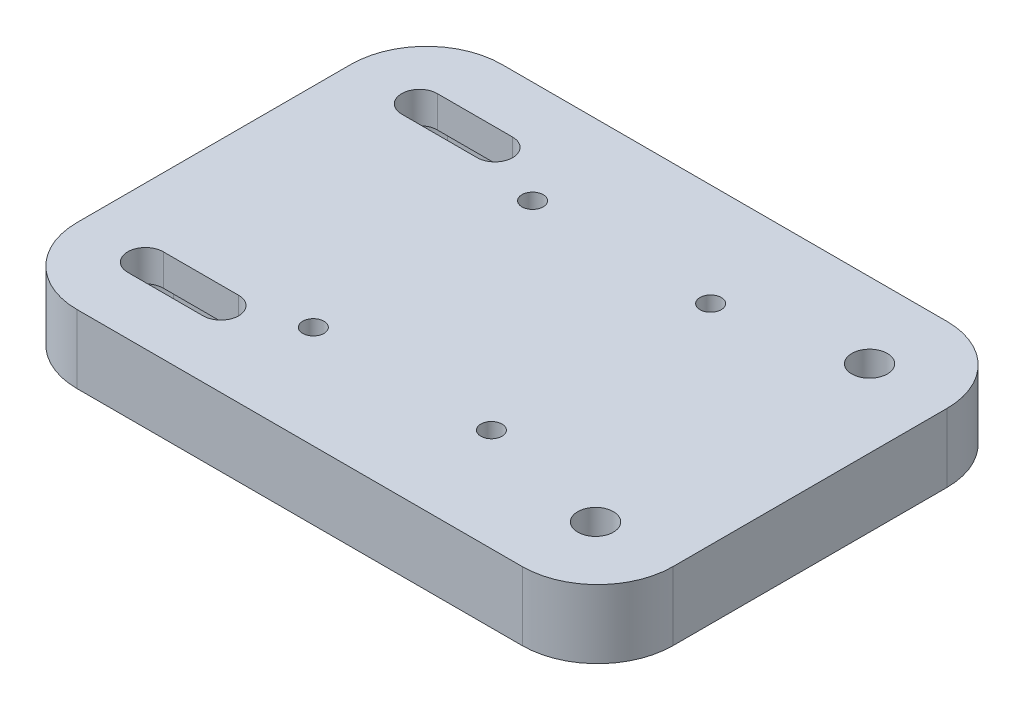
SolidWorks part; units mm, degrees
material "ABS"
ref_plane "Front Plane" through (0, 0, 0) normal (0, 0, 1) x (1, 0, 0)
ref_plane "Top Plane" through (0, 0, 0) normal (0, 1, 0) x (1, 0, 0)
ref_plane "Right Plane" through (0, 0, 0) normal (1, 0, 0) x (0, 0, -1)
sketch "Sketch1" plane through (0, 0, 0) normal (0, 1, 0) x (1, 0, 0)
  line L0 (0, 11) -> (0, 51)
  line L1 (11, 62) -> (76, 62)
  line L2 (87, 51) -> (87, 11)
  line L3 (76, 0) -> (11, 0)
  line L4 (0, 11) -> (0, 0) construction
  line L5 (0, 0) -> (11, 0) construction
  arc A0 (11, 62) -> (0, 51) centre (11, 51) ccw
  arc A1 (0, 11) -> (11, 0) centre (11, 11) ccw
  arc A2 (76, 0) -> (87, 11) centre (76, 11) ccw
  arc A3 (87, 51) -> (76, 62) centre (76, 51) ccw
  dimension "D3" = 22
  dimension "D1" = 87
  dimension "D2" = 62
extrude "Boss-Extrude1" add sketch "Sketch1" along normal blind 10
sketch "Sketch8" plane through (0, 10, 0) normal (0, 1, 0) x (1, 0, 0)
  line L0 (76, 62) -> (11, 62) construction
  line L1 (0, 51) -> (0, 11) construction
  line L2 (11, 0) -> (76, 0) construction
  line L3 (10, 53.6) -> (21, 53.6)
  line L4 (10, 48.4) -> (21, 48.4)
  line L5 (10, 13.6) -> (21, 13.6)
  line L6 (21, 8.4) -> (10, 8.4)
  circle A0 centre (75.7, 51) radius 2.6
  circle A1 centre (75.7, 11) radius 2.6
  arc A2 (21, 48.4) -> (21, 53.6) centre (21, 51) ccw
  arc A3 (10, 53.6) -> (10, 48.4) centre (10, 51) ccw
  arc A4 (21, 8.4) -> (21, 13.6) centre (21, 11) ccw
  arc A5 (10, 13.6) -> (10, 8.4) centre (10, 11) ccw
  point P11 (43.5, 62)
  dimension "D1" = 5.2
  dimension "D2" = 11
  dimension "D3" = 10
  dimension "D4" = 32.2
  dimension "D5" = 11
  dimension "D6" = 11
extrude "Cut-Extrude5" cut sketch "Sketch8" against normal up to next
sketch "Sketch9" plane through (0, 0, 0) normal (0, -1, 0) x (1, 0, 0)
  line L0 (10, -6.9) -> (21, -6.9)
  line L1 (21, -15.1) -> (10, -15.1)
  line L2 (10, -46.9) -> (21, -46.9)
  line L3 (21, -55.1) -> (10, -55.1)
  line L4 (6.959, -13.75) -> (3, -13.75)
  line L5 (3, -13.75) -> (3, -8.25)
  line L6 (3, -8.25) -> (6.959, -8.25)
  line L7 (6.959, -53.75) -> (3, -53.75)
  line L8 (3, -53.75) -> (3, -48.25)
  line L9 (0, -51) -> (0, -11) construction
  line L10 (3, -48.25) -> (6.959, -48.25)
  circle A0 centre (75.7, -11) radius 4.1
  circle A1 centre (75.7, -51) radius 4.1
  arc A2 (21, -55.1) -> (21, -46.9) centre (21, -51) ccw
  arc A3 (10, -46.9) -> (6.959, -48.25) centre (10, -51) ccw
  arc A4 (21, -15.1) -> (21, -6.9) centre (21, -11) ccw
  arc A5 (10, -6.9) -> (6.959, -8.25) centre (10, -11) ccw
  arc A6 (6.959, -53.75) -> (10, -55.1) centre (10, -51) ccw
  arc A7 (6.959, -13.75) -> (10, -15.1) centre (10, -11) ccw
  dimension "D1" = 8.2
  dimension "D2" = 5.5
  dimension "D3" = 3
  dimension "D4" = 3
extrude "Cut-Extrude6" cut sketch "Sketch9" against normal blind 5.4
sketch "Sketch11" plane through (0, 0, 0) normal (-1, 0, 0) x (0, 0, 1)
  line L0 (-11, 10) -> (-11, 0) construction
  line L1 (-51, 10) -> (-51, 0) construction
  circle A0 centre (-11, 5) radius 1.6
  circle A1 centre (-51, 5) radius 1.6
  dimension "D1" = 3.2
extrude "Cut-Extrude7" cut sketch "Sketch11" against normal up to next
sketch "Sketch12" plane through (3, 0, 0) normal (1, 0, 0) x (0, 0, -1)
  line L1 (48.25, 6.5877) -> (48.25, 3.4123)
  line L2 (48.25, 3.4123) -> (51, 1.8246)
  line L3 (51, 1.8246) -> (53.75, 3.4123)
  line L4 (53.75, 3.4123) -> (53.75, 6.5877)
  line L5 (53.75, 6.5877) -> (51, 8.1754)
  line L6 (51, 8.1754) -> (48.25, 6.5877)
  line L7 (13.75, 3.4123) -> (13.75, 6.5877)
  line L8 (13.75, 6.5877) -> (11, 8.1754)
  line L9 (11, 8.1754) -> (8.25, 6.5877)
  line L10 (8.25, 6.5877) -> (8.25, 3.4123)
  line L11 (8.25, 3.4123) -> (11, 1.8246)
  line L12 (11, 1.8246) -> (13.75, 3.4123)
  circle A0 centre (51, 5) radius 2.75 construction
  circle A1 centre (11, 5) radius 2.75 construction
  dimension "D1" = 5.5
  dimension "D2" = 5.5
extrude "Cut-Extrude8" cut sketch "Sketch12" along normal blind 3
sketch "Sketch14" plane through (0, 10, 0) normal (0, 1, 0) x (1, 0, 0)
  line L0 (76, 62) -> (11, 62) construction
  line L1 (0, 51) -> (0, 11) construction
  circle A0 centre (30.5, 47) radius 1.55
  circle A1 centre (56.5, 47) radius 1.55
  circle A2 centre (30.5, 15) radius 1.55
  circle A3 centre (56.5, 15) radius 1.55
  point P8 (43.5, 62)
  point P11 (0, 31)
  dimension "D1" = 3.1
  dimension "D2" = 26
  dimension "D3" = 32
  dimension "D4" = 13
  dimension "D5" = 16
extrude "Cut-Extrude9" cut sketch "Sketch14" against normal up to next
sketch "Sketch15" plane through (0, 0, 0) normal (0, -1, 0) x (1, 0, 0)
  line L1 (33.7332, -15) -> (32.1166, -12.2)
  line L2 (32.1166, -12.2) -> (28.8834, -12.2)
  line L3 (28.8834, -12.2) -> (27.2668, -15)
  line L4 (27.2668, -15) -> (28.8834, -17.8)
  line L5 (28.8834, -17.8) -> (32.1166, -17.8)
  line L6 (32.1166, -17.8) -> (33.7332, -15)
  line L7 (59.7332, -15) -> (58.1166, -12.2)
  line L8 (58.1166, -12.2) -> (54.8834, -12.2)
  line L9 (54.8834, -12.2) -> (53.2668, -15)
  line L10 (53.2668, -15) -> (54.8834, -17.8)
  line L11 (54.8834, -17.8) -> (58.1166, -17.8)
  line L12 (58.1166, -17.8) -> (59.7332, -15)
  line L13 (59.7332, -47) -> (58.1166, -44.2)
  line L14 (58.1166, -44.2) -> (54.8834, -44.2)
  line L15 (54.8834, -44.2) -> (53.2668, -47)
  line L16 (53.2668, -47) -> (54.8834, -49.8)
  line L17 (54.8834, -49.8) -> (58.1166, -49.8)
  line L18 (58.1166, -49.8) -> (59.7332, -47)
  line L19 (33.7332, -47) -> (32.1166, -44.2)
  line L20 (32.1166, -44.2) -> (28.8834, -44.2)
  line L21 (28.8834, -44.2) -> (27.2668, -47)
  line L22 (27.2668, -47) -> (28.8834, -49.8)
  line L23 (28.8834, -49.8) -> (32.1166, -49.8)
  line L24 (32.1166, -49.8) -> (33.7332, -47)
  circle A0 centre (30.5, -15) radius 2.8 construction
  circle A1 centre (56.5, -15) radius 2.8 construction
  circle A2 centre (56.5, -47) radius 2.8 construction
  circle A3 centre (30.5, -47) radius 2.8 construction
  dimension "D1" = 5.6
extrude "Cut-Extrude10" cut sketch "Sketch15" against normal blind 2.6
equation "\"D5@Sketch8\"=\"D2@Sketch8\""
equation "\"D2@Sketch12\"=\"D1@Sketch12\""
equation "\"D4@Sketch14\"=\"D2@Sketch14\"/2"
equation "\"D5@Sketch14\"=\"D3@Sketch14\"/2"
